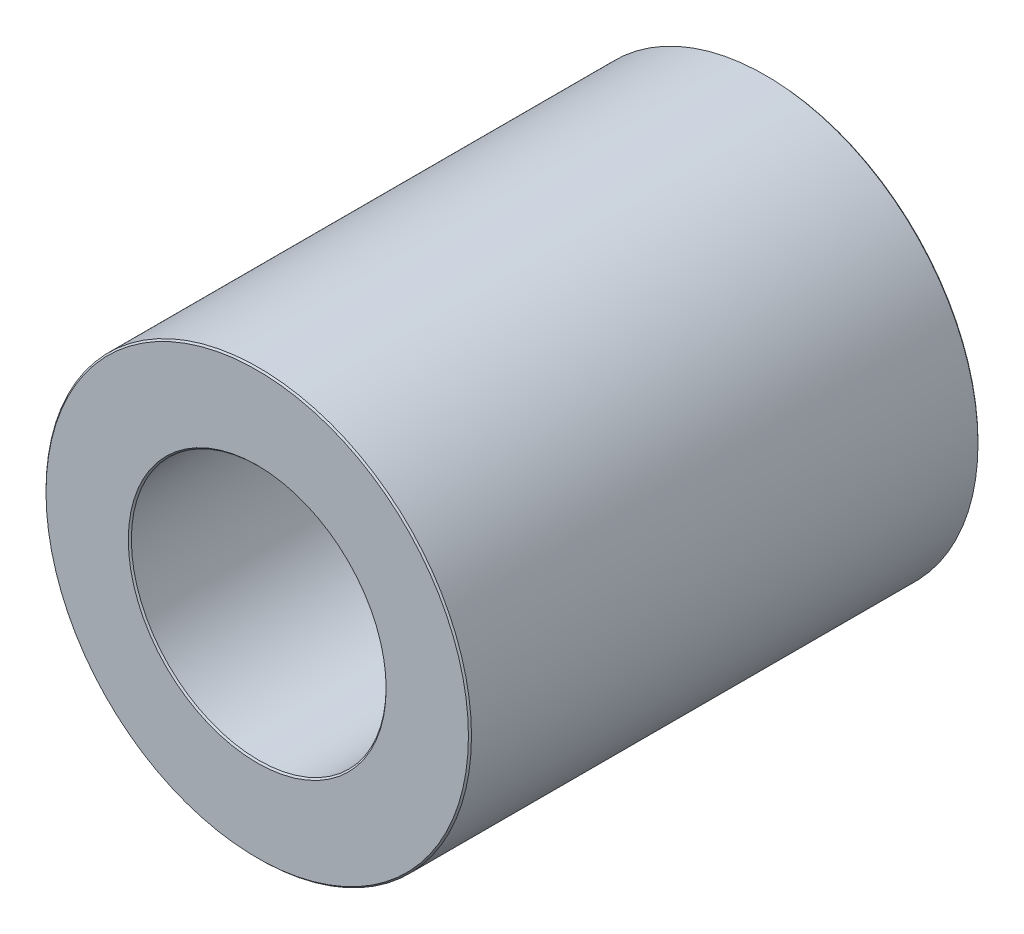
SolidWorks part; units mm, degrees
material "841 Oilite Bronze"
ref_plane "Front Plane" through (0, 0, 0) normal (0, 0, 1) x (1, 0, 0)
ref_plane "Top Plane" through (0, 0, 0) normal (0, 1, 0) x (1, 0, 0)
ref_plane "Right Plane" through (0, 0, 0) normal (1, 0, 0) x (0, 0, -1)
sketch "Sketch1" plane through (0, 0, 0) normal (0, 0, 1) x (1, 0, 0)
  circle A0 centre (0, 0) radius 5.01
  circle A1 centre (0, 0) radius 3
  point P8 (0, -5.01)
  point P9 (0, 5.01)
  dimension "ID" = 6
  dimension "OD" = 10.02
sketch "Sketch2" plane through (0, 0, 0) normal (1, 0, 0) x (0, 0, -1)
  line L0 (6, 0) -> (-6, 0) construction
  line L1 (6, 5.01) -> (-6, 5.01) construction
  point P4 (0, 0)
  point P8 (0, 5.01)
  point P9 (0, 5.01)
  dimension "Length" = 12
sketch "Sketch5" plane through (0, 0, 0) normal (0, 0, 1) x (1, 0, 0)
  circle A0 centre (0, 0) radius 3 construction
  circle A1 centre (0, 0) radius 5.01 construction
  circle A2 centre (0, 0) radius 3
  circle A3 centre (0, 0) radius 5.01
extrude "Boss-Extrude1" add sketch "Sketch5" along normal up to vertex (6 mm away) and the other way up to vertex (6 mm away) up to point (0, 0, 6) other way up to point (0, 0, -6)
chamfer "Chamfer1" distance 0.036 angle 45 4 edges at (5.01, 0, -6) (3, 0, -6) (3, 0, 6) (5.01, 0, 6)
equation "\"D1@Chamfer1\"=\"ID@Sketch1\"*.006"
